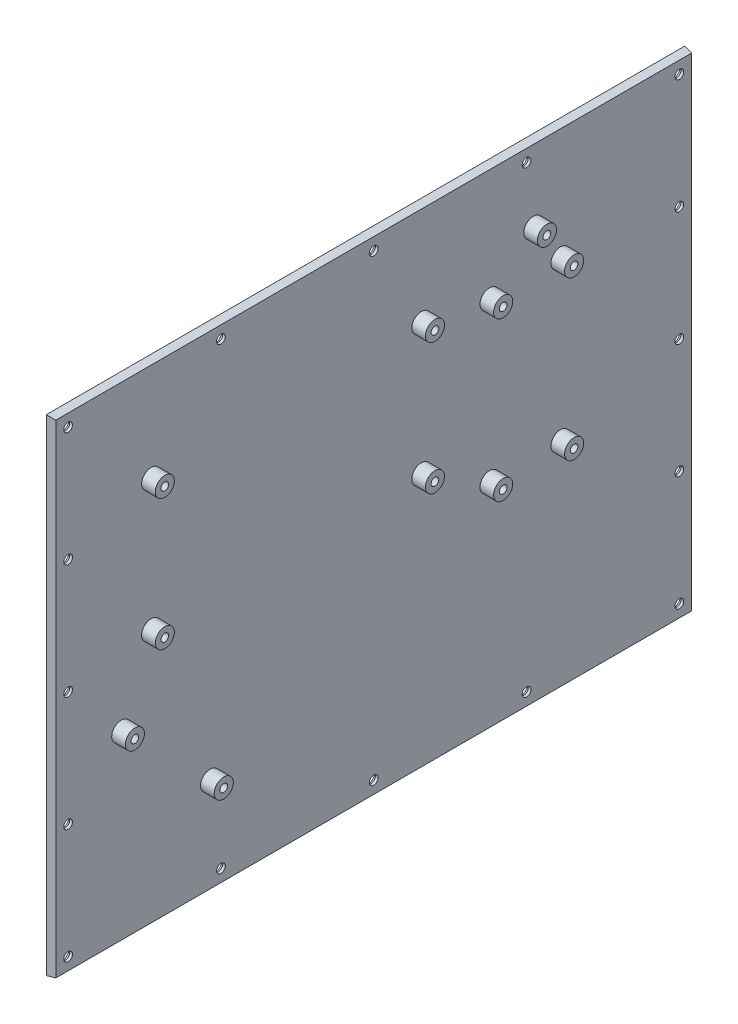
SolidWorks part; units mm, degrees
ref_plane "Front Plane" through (0, 0, 0) normal (0, 0, 1) x (1, 0, 0)
ref_plane "Top Plane" through (0, 0, 0) normal (0, 1, 0) x (1, 0, 0)
ref_plane "Right Plane" through (0, 0, 0) normal (1, 0, 0) x (0, 0, -1)
sketch "Sketch1" plane through (0, 0, 0) normal (1, 0, 0) x (0, 0, -1)
  line L1 (117, 89) -> (-117, 89)
  line L2 (117, 89) -> (117, -89)
  line L3 (117, -89) -> (-117, -89)
  line L4 (-117, 89) -> (-117, -89)
  line L5 (117, 89) -> (-117, -89) construction
  line L6 (117, -89) -> (-117, 89) construction
  point P0 (0, 0)
  dimension "D1" = 234
  dimension "D2" = 178
extrude "Boss-Extrude1" add sketch "Sketch1" along normal blind 3 draft 9
sketch "Sketch2" plane through (3, 0, 0) normal (1, 0, 0) x (0, 0, -1)
  line L0 (116.5248, 88.5248) -> (-116.5248, 88.5248) construction
  line L1 (62.4752, 68.5248) -> (-96.5248, 68.5248) construction
  line L2 (62.4752, 68.5248) -> (62.4752, -28.4752) construction
  line L3 (62.4752, -28.4752) -> (-96.5248, -28.4752) construction
  line L4 (-96.5248, 68.5248) -> (-96.5248, -28.4752) construction
  line L5 (62.4752, 68.5248) -> (-96.5248, -28.4752) construction
  line L6 (62.4752, -28.4752) -> (-96.5248, 68.5248) construction
  line L7 (-116.5248, 88.5248) -> (-116.5248, -88.5248) construction
  line L8 (-117, -89) -> (117, -89) construction
  line L9 (68.4363, 47.5311) -> (42.4363, 47.5311) construction
  line L10 (68.4363, 47.5311) -> (68.4363, -10.4689) construction
  line L11 (68.4363, -10.4689) -> (42.4363, -10.4689) construction
  line L12 (42.4363, 47.5311) -> (42.4363, -10.4689) construction
  line L13 (68.4363, 47.5311) -> (42.4363, -10.4689) construction
  line L14 (68.4363, -10.4689) -> (42.4363, 47.5311) construction
  line L15 (-81.5637, 52.5248) -> (17.4363, 52.5248) construction
  line L16 (-81.5637, 52.5248) -> (-81.5637, 4.5248) construction
  line L17 (-81.5637, 4.5248) -> (17.4363, 4.5248) construction
  line L18 (17.4363, 52.5248) -> (17.4363, 4.5248) construction
  line L19 (-81.5637, 52.5248) -> (17.4363, 4.5248) construction
  line L20 (-81.5637, 4.5248) -> (17.4363, 52.5248) construction
  circle A0 centre (-92.5248, -22.1752) radius 1.4
  circle A1 centre (-92.5248, -22.1752) radius 3.5
  circle A2 centre (58.4752, 62.2248) radius 1.4
  circle A3 centre (58.4752, 62.2248) radius 3.5
  circle A4 centre (-81.5637, 52.5248) radius 1.4
  circle A5 centre (17.4363, 52.5248) radius 1.4
  circle A6 centre (17.4363, 4.5248) radius 1.4
  circle A7 centre (-81.5637, 4.5248) radius 1.4
  circle A8 centre (68.4363, -10.4689) radius 1.4
  circle A9 centre (42.4363, -10.4689) radius 1.4
  circle A10 centre (42.4363, 47.5311) radius 1.4
  circle A11 centre (68.4363, 47.5311) radius 1.4
  circle A12 centre (-81.5637, 52.5248) radius 3.5
  circle A13 centre (17.4363, 52.5248) radius 3.5
  circle A14 centre (42.4363, 47.5311) radius 3.5
  circle A15 centre (68.4363, 47.5311) radius 3.5
  circle A16 centre (42.4363, -10.4689) radius 3.5
  circle A17 centre (68.4363, -10.4689) radius 3.5
  circle A18 centre (17.4363, 4.5248) radius 3.5
  circle A19 centre (-81.5637, 4.5248) radius 3.5
  circle A20 centre (-59.9649, -54) radius 1.4
  circle A21 centre (-59.9649, -54) radius 3.5
  point P0 (-17.0248, 20.0248)
  point P15 (-32.0637, 28.5248)
  point P19 (55.4363, 18.5311)
  dimension "D5" = 2.8
  dimension "D6" = 7
  dimension "D1" = 159
  dimension "D2" = 97
  dimension "D3" = 20
  dimension "D4" = 20
  dimension "D7" = 6.3
  dimension "D8" = 6.3
  dimension "D9" = 4
  dimension "D10" = 4
  dimension "D11" = 26
  dimension "D12" = 58
  dimension "D13" = 99
  dimension "D14" = 48
  dimension "D15" = 60
  dimension "D16" = 25
  dimension "D17" = 35
extrude "Boss-Extrude2" add sketch "Sketch2" along normal blind 5
sketch "Sketch3" plane through (0, 0, 0) normal (-1, 0, 0) x (0, 0, 1)
  line L0 (-117, -89) -> (-117, 89) construction
  line L1 (-117, 89) -> (117, 89) construction
  line L2 (-117, 0) -> (117, 0) construction
  line L3 (117, 89) -> (117, -89) construction
  circle A0 centre (-112, 84) radius 1.6
  circle A2 centre (-56, 84) radius 1.6
  circle A3 centre (0, 84) radius 1.6
  circle A4 centre (56, 84) radius 1.6
  circle A5 centre (112, 84) radius 1.6
  circle A6 centre (112, 42) radius 1.6
  circle A7 centre (112, 0) radius 1.6
  circle A8 centre (112, -42) radius 1.6
  circle A9 centre (112, -84) radius 1.6
  circle A10 centre (56, -84) radius 1.6
  circle A11 centre (0, -84) radius 1.6
  circle A12 centre (-56, -84) radius 1.6
  circle A13 centre (-112, -84) radius 1.6
  circle A14 centre (-112, 42) radius 1.6
  circle A15 centre (-112, 0) radius 1.6
  circle A16 centre (-112, -42) radius 1.6
  dimension "D1" = 3.2
  dimension "D2" = 5
  dimension "D3" = 5
  dimension "D5" = 5
  dimension "D6" = 5
  dimension "D4" = 4
extrude "Cut-Extrude1" cut sketch "Sketch3" against normal up to surface (3 mm away) up to face at (3, -54, 63.4649)
chamfer "Chamfer1" distance 2 angle 45 16 edges at (0, -84, -57.6) (0, -84, -1.6) (0, -84, 54.4) (0, -84, 110.4) (0, -42, 113.6) (0, 0, 113.6) (0, 42, 113.6) (0, 84, 113.6) (0, 84, 57.6) (0, 84, 1.6) (0, 84, -54.4) (0, -84, -113.6) (0, -42, -110.4) (0, 0, -110.4) (0, 42, -110.4) (0, 84, -110.4)
